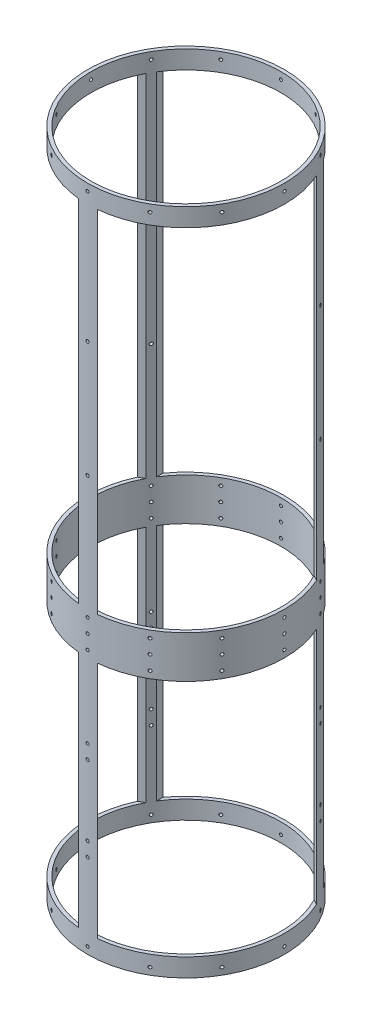
SolidWorks part; units mm, degrees
material "6061-T6 (SS)"
ref_plane "Front Plane" through (0, 0, 0) normal (0, 0, 1) x (1, 0, 0)
ref_plane "Top Plane" through (0, 0, 0) normal (0, 1, 0) x (1, 0, 0)
ref_plane "Right Plane" through (0, 0, 0) normal (1, 0, 0) x (0, 0, -1)
sketch "Sketch1" plane through (0, 0, 0) normal (0, 1, 0) x (1, 0, 0)
  circle A0 centre (0, 0) radius 88.9
  circle A1 centre (0, 0) radius 85.725
  dimension "D1" = 177.8
  dimension "D2" = 171.45
extrude "Boss-Extrude1" add sketch "Sketch1" along normal mid plane 603.25
sketch "Sketch2" plane through (0, 0, 0) normal (0, 0, 1) x (1, 0, 0)
  line L0 (88.9, -301.625) -> (88.9, 301.625) construction
  line L5 (-88.9, -301.625) -> (88.9, -301.625) construction
  line L6 (72.39, -285.115) -> (-72.39, -285.115)
  line L7 (-88.9, 301.625) -> (-88.9, -301.625) construction
  line L9 (72.39, -285.115) -> (72.39, -69.723)
  line L10 (72.39, -69.723) -> (-72.39, -69.723)
  line L11 (-72.39, -285.115) -> (-72.39, -69.723)
  line L12 (85.725, 301.625) -> (-85.725, 301.625) construction
  line L13 (72.39, -31.623) -> (-72.39, -31.623)
  line L14 (72.39, -31.623) -> (72.39, 285.115)
  line L15 (72.39, 285.115) -> (-72.39, 285.115)
  line L16 (-72.39, -31.623) -> (-72.39, 285.115)
  dimension "D1" = 16.51
  dimension "D2" = 16.51
  dimension "D3" = 16.51
  dimension "D4" = 231.902
  dimension "D5" = 16.51
  dimension "D6" = 38.1
extrude "Cut-Extrude1" cut sketch "Sketch2" against normal up to surface (51.6033 mm away)
pattern_circular "CirPattern1" count 3 over 360 about axis through (0, 0, 0) along (0, 1, 0) of "Cut-Extrude1"
ref_plane "Plane1" through (0, 0, 88.9) normal (0, 0, 1) x (1, 0, 0)
sketch "Sketch3" plane through (0, 0, 88.9) normal (0, 0, 1) x (1, 0, 0)
  line L0 (0, -97.79) -> (0, 97.79) construction
  line L1 (88.9, 301.625) -> (-88.9, 301.625) construction
  circle A0 centre (0, 295.275) radius 1.3526
  dimension "D1" = 2.7051
  dimension "D2" = 6.35
extrude "Cut-Extrude2" cut sketch "Sketch3" against normal blind 25.908
pattern_circular "CirPattern2" count 12 over 360 about axis through (0, 301.625, 0) along (0, -1, 0) of "Cut-Extrude2"
mirror "Mirror1" about plane through (0, 0, 0) normal (0, 1, 0) of "CirPattern2", "Cut-Extrude2"
sketch "Sketch4" plane through (0, 0, 88.9) normal (0, 0, 1) x (1, 0, 0)
  line L0 (0, -97.79) -> (0, 97.79) construction
  circle A0 centre (0, -225.425) radius 1.3525
  circle A1 centre (0, -212.725) radius 1.3525
  circle A2 centre (0, -295.275) radius 1.3526 construction
  circle A3 centre (0, -149.225) radius 1.3525
  circle A4 centre (0, -136.525) radius 1.3525
  dimension "D1" = 69.85
  dimension "D2" = 2.7051
  dimension "D3" = 12.7
  dimension "D4" = 2.7051
  dimension "D5" = 63.5
  dimension "D6" = 12.7
  dimension "D7" = 2.7051
  dimension "D8" = 2.7051
extrude "Cut-Extrude3" cut sketch "Sketch4" against normal blind 34.798
pattern_circular "CirPattern3" count 3 over 360 about axis through (0, 301.625, 0) along (0, -1, 0) of "Cut-Extrude3"
sketch "Sketch5" plane through (0, 0, 88.9) normal (0, 0, 1) x (1, 0, 0)
  line L0 (0, -97.79) -> (0, 97.79) construction
  line L1 (-8.4947, -31.623) -> (-88.9, -31.623) construction
  line L2 (-88.9, -69.723) -> (-8.4947, -69.723) construction
  line L3 (88.9, -31.623) -> (8.4947, -31.623) construction
  circle A0 centre (0, -50.673) radius 1.3526
  circle A1 centre (0, 73.025) radius 1.4351
  circle A2 centre (0, 177.927) radius 1.4351
  circle A3 centre (0, 295.275) radius 1.3526 construction
  circle A4 centre (0, -37.973) radius 1.3526
  circle A5 centre (0, -63.373) radius 1.3526
  dimension "D1" = 2.7051
  dimension "D3" = 117.348
  dimension "D5" = 2.8702
  dimension "D6" = 2.8702
  dimension "D4" = 123.698
  dimension "D7" = 2.7051
  dimension "D8" = 2.7051
  dimension "D9" = 6.35
  dimension "D10" = 6.35
  dimension "D2" = 19.05
extrude "Cut-Extrude4" cut sketch "Sketch5" against normal blind 87.63
pattern_circular "CirPattern4" count 12 over 360 about axis through (0, 301.625, 0) along (0, -1, 0) of "Cut-Extrude4"
